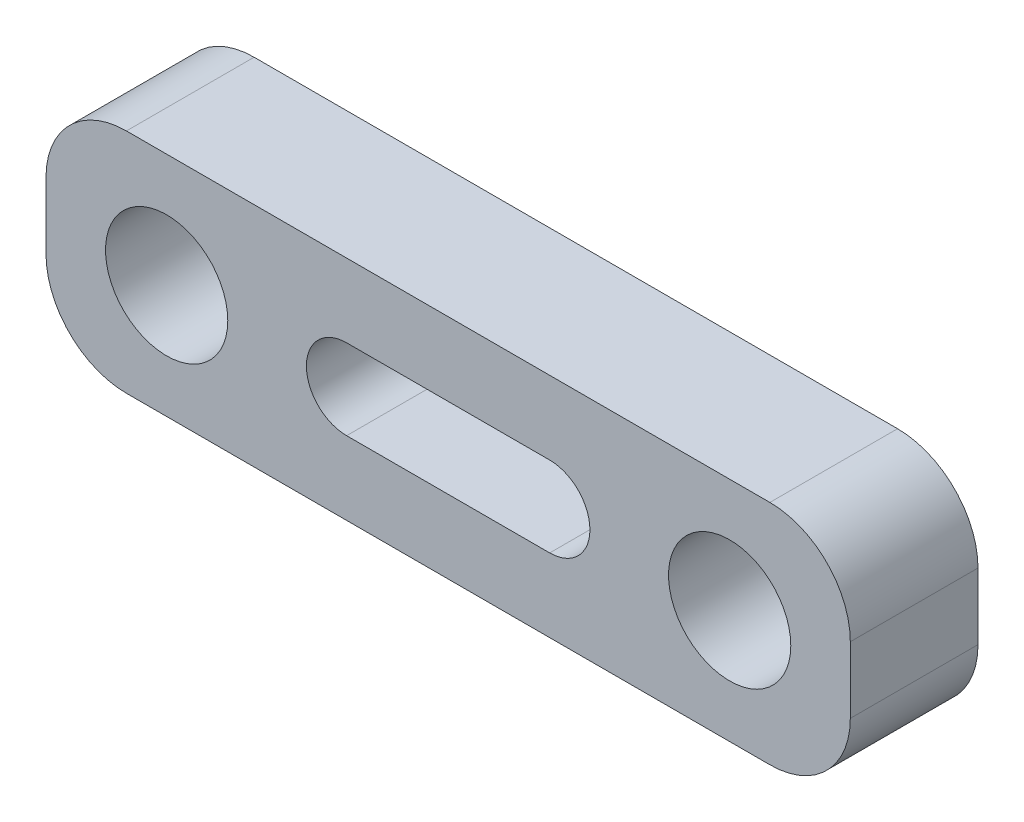
SolidWorks part; units mm, degrees
ref_plane "Front Plane" through (0, 0, 0) normal (0, 0, 1) x (1, 0, 0)
ref_plane "Top Plane" through (0, 0, 0) normal (0, 1, 0) x (1, 0, 0)
ref_plane "Right Plane" through (0, 0, 0) normal (1, 0, 0) x (0, 0, -1)
sketch "Sketch1" plane through (0, 0, 0) normal (0, 0, 1) x (1, 0, 0)
  line L1 (-10, -2.825) -> (10, -2.825)
  line L2 (-10, -2.825) -> (-10, 2.825)
  line L3 (-10, 2.825) -> (10, 2.825)
  line L4 (10, -2.825) -> (10, 2.825)
  line L5 (-10, -2.825) -> (10, 2.825) construction
  line L6 (-10, 2.825) -> (10, -2.825) construction
  point P0 (0, 0)
extrude "Boss-Extrude1" add sketch "Sketch1" along normal blind 3.175
fillet "Fillet1" radius 2 4 edges at (10, -2.825, 1.5875) (10, 2.825, 1.5875) (-10, -2.825, 1.5875) (-10, 2.825, 1.5875)
sketch "Sketch2" plane through (0, 0, 3.175) normal (0, 0, 1) x (1, 0, 0)
  line L0 (0, 0) -> (-7, 0) construction
  line L1 (-2.525, 0) -> (2.525, 0) construction
  line L2 (-2.525, 1) -> (2.525, 1)
  line L3 (-2.525, -1) -> (2.525, -1)
  line L4 (0, 0) -> (7, 0) construction
  arc A0 (-2.525, 1) -> (-2.525, -1) centre (-2.525, 0) ccw
  arc A1 (2.525, -1) -> (2.525, 1) centre (2.525, 0) ccw
  circle A2 centre (-7, 0) radius 1.52
  circle A3 centre (7, 0) radius 1.52
  point P4 (0, 0)
extrude "Cut-Extrude1" cut sketch "Sketch2" against normal blind 3.175
